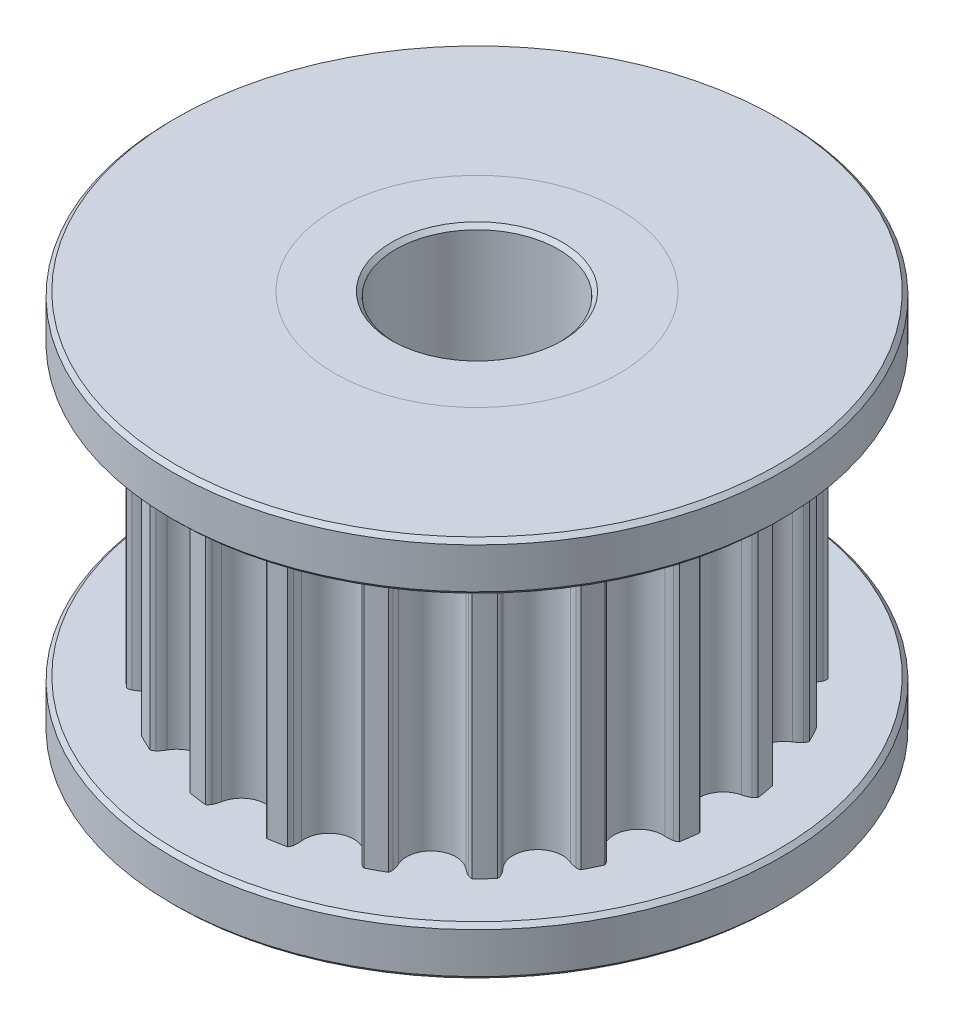
SolidWorks part; units mm, degrees
material "7075-T6 (SN)"
ref_plane "Přední rovina" through (0, 0, 0) normal (0, 0, 1) x (1, 0, 0)
ref_plane "Horní rovina" through (0, 0, 0) normal (0, 1, 0) x (1, 0, 0)
ref_plane "Pravá rovina" through (0, 0, 0) normal (1, 0, 0) x (0, 0, -1)
sketch "Skica1" plane through (0, 0, 0) normal (0, 1, 0) x (1, 0, 0)
  circle A0 centre (0, 0) radius 2
  arc B0 (-5.7301, 1.0983) -> (-5.3872, 2.2403) centre (-5.6803, 1.7058) ccw
  arc B1 (-5.7301, 1.0983) -> (-5.922, 1.0859) centre (-5.7841, 0.4401) ccw
  arc B2 (-5.922, 1.0859) -> (-6.0197, 1.0387) centre (-5.8743, 0.8624) ccw
  arc B3 (-6.0197, 1.0387) -> (-6.0791, 0.6004) centre (0, 0) ccw
  arc B4 (-6.0791, 0.6004) -> (-5.9974, 0.5289) centre (-5.892, 0.7317) ccw
  arc B5 (-5.9974, 0.5289) -> (-5.8158, 0.466) centre (-5.6927, 1.1148) ccw
  arc B6 (-5.7891, -0.7262) -> (-5.8158, 0.466) centre (-5.9294, -0.133) ccw
  arc B7 (-5.7891, -0.7262) -> (-5.9677, -0.7972) centre (-5.637, -1.3689) ccw
  arc B8 (-5.9677, -0.7972) -> (-6.0461, -0.8723) centre (-5.8532, -0.9951) ccw
  arc B9 (-6.0461, -0.8723) -> (-5.9671, -1.3075) centre (0, 0) ccw
  arc B10 (-5.9671, -1.3075) -> (-5.8673, -1.3503) centre (-5.8297, -1.1248) ccw
  arc B11 (-5.8673, -1.3503) -> (-5.6751, -1.354) centre (-5.7586, -0.6989) ccw
  arc B12 (-5.2813, -2.4796) -> (-5.6751, -1.354) centre (-5.5981, -1.9587) ccw
  arc B13 (-5.2813, -2.4796) -> (-5.4293, -2.6023) centre (-4.9381, -3.0438) ccw
  arc B14 (-5.4293, -2.6023) -> (-5.4806, -2.698) centre (-5.2593, -2.7551) ccw
  arc B15 (-5.4806, -2.698) -> (-5.271, -3.0875) centre (0, 0) ccw
  arc B16 (-5.271, -3.0875) -> (-5.1629, -3.0973) centre (-5.1968, -2.8713) ccw
  arc B17 (-5.1629, -3.0973) -> (-4.979, -3.0415) centre (-5.2608, -2.4442) ccw
  arc B18 (-4.2566, -3.9902) -> (-4.979, -3.0415) centre (-4.7188, -3.5928) ccw
  arc B19 (-4.2566, -3.9902) -> (-4.3594, -4.1527) centre (-3.7559, -4.4208) ccw
  arc B20 (-4.3594, -4.1527) -> (-4.3786, -4.2595) centre (-4.1505, -4.2455) ccw
  arc B21 (-4.3786, -4.2595) -> (-4.059, -4.5652) centre (0, 0) ccw
  arc B22 (-4.059, -4.5652) -> (-3.9531, -4.5412) centre (-4.0552, -4.3366) ccw
  arc B23 (-3.9531, -4.5412) -> (-3.7954, -4.4312) centre (-4.248, -3.9503) ccw
  arc B24 (-2.8152, -5.1103) -> (-3.7954, -4.4312) centre (-3.3776, -4.8751) ccw
  arc B25 (-2.8152, -5.1103) -> (-2.8628, -5.2965) centre (-2.2059, -5.3651) ccw
  arc B26 (-2.8628, -5.2965) -> (-2.8481, -5.4041) centre (-2.6354, -5.3203) ccw
  arc B27 (-2.8481, -5.4041) -> (-2.4496, -5.596) centre (0, 0) ccw
  arc B28 (-2.4496, -5.596) -> (-2.3563, -5.5405) centre (-2.5166, -5.3775) ccw
  arc B29 (-2.3563, -5.5405) -> (-2.2403, -5.3872) centre (-2.8194, -5.0696) ccw
  arc B30 (-1.0983, -5.7301) -> (-2.2403, -5.3872) centre (-1.7058, -5.6803) ccw
  arc B31 (-1.0983, -5.7301) -> (-1.0859, -5.922) centre (-0.4401, -5.7841) ccw
  arc B32 (-1.0859, -5.922) -> (-1.0387, -6.0197) centre (-0.8624, -5.8743) ccw
  arc B33 (-1.0387, -6.0197) -> (-0.6004, -6.0791) centre (0, 0) ccw
  arc B34 (-0.6004, -6.0791) -> (-0.5289, -5.9974) centre (-0.7317, -5.892) ccw
  arc B35 (-0.5289, -5.9974) -> (-0.466, -5.8158) centre (-1.1148, -5.6927) ccw
  arc B36 (0.7262, -5.7891) -> (-0.466, -5.8158) centre (0.133, -5.9294) ccw
  arc B37 (0.7262, -5.7891) -> (0.7972, -5.9677) centre (1.3689, -5.637) ccw
  arc B38 (0.7972, -5.9677) -> (0.8723, -6.0461) centre (0.9951, -5.8532) ccw
  arc B39 (0.8723, -6.0461) -> (1.3075, -5.9671) centre (0, 0) ccw
  arc B40 (1.3075, -5.9671) -> (1.3503, -5.8673) centre (1.1248, -5.8297) ccw
  arc B41 (1.3503, -5.8673) -> (1.354, -5.6751) centre (0.6989, -5.7586) ccw
  arc B42 (2.4796, -5.2813) -> (1.354, -5.6751) centre (1.9587, -5.5981) ccw
  arc B43 (2.4796, -5.2813) -> (2.6023, -5.4293) centre (3.0438, -4.9381) ccw
  arc B44 (2.6023, -5.4293) -> (2.698, -5.4806) centre (2.7551, -5.2593) ccw
  arc B45 (2.698, -5.4806) -> (3.0875, -5.271) centre (0, 0) ccw
  arc B46 (3.0875, -5.271) -> (3.0973, -5.1629) centre (2.8713, -5.1968) ccw
  arc B47 (3.0973, -5.1629) -> (3.0415, -4.979) centre (2.4442, -5.2608) ccw
  arc B48 (3.9902, -4.2566) -> (3.0415, -4.979) centre (3.5928, -4.7188) ccw
  arc B49 (3.9902, -4.2566) -> (4.1527, -4.3594) centre (4.4208, -3.7559) ccw
  arc B50 (4.1527, -4.3594) -> (4.2595, -4.3786) centre (4.2455, -4.1505) ccw
  arc B51 (4.2595, -4.3786) -> (4.5652, -4.059) centre (0, 0) ccw
  arc B52 (4.5652, -4.059) -> (4.5412, -3.9531) centre (4.3366, -4.0552) ccw
  arc B53 (4.5412, -3.9531) -> (4.4312, -3.7954) centre (3.9503, -4.248) ccw
  arc B54 (5.1103, -2.8152) -> (4.4312, -3.7954) centre (4.8751, -3.3776) ccw
  arc B55 (5.1103, -2.8152) -> (5.2965, -2.8628) centre (5.3651, -2.2059) ccw
  arc B56 (5.2965, -2.8628) -> (5.4041, -2.8481) centre (5.3203, -2.6354) ccw
  arc B57 (5.4041, -2.8481) -> (5.596, -2.4496) centre (0, 0) ccw
  arc B58 (5.596, -2.4496) -> (5.5405, -2.3563) centre (5.3775, -2.5166) ccw
  arc B59 (5.5405, -2.3563) -> (5.3872, -2.2403) centre (5.0696, -2.8194) ccw
  arc B60 (5.7301, -1.0983) -> (5.3872, -2.2403) centre (5.6803, -1.7058) ccw
  arc B61 (5.7301, -1.0983) -> (5.922, -1.0859) centre (5.7841, -0.4401) ccw
  arc B62 (5.922, -1.0859) -> (6.0197, -1.0387) centre (5.8743, -0.8624) ccw
  arc B63 (6.0197, -1.0387) -> (6.0791, -0.6004) centre (0, 0) ccw
  arc B64 (6.0791, -0.6004) -> (5.9974, -0.5289) centre (5.892, -0.7317) ccw
  arc B65 (5.9974, -0.5289) -> (5.8158, -0.466) centre (5.6927, -1.1148) ccw
  arc B66 (5.7891, 0.7262) -> (5.8158, -0.466) centre (5.9294, 0.133) ccw
  arc B67 (5.7891, 0.7262) -> (5.9677, 0.7972) centre (5.637, 1.3689) ccw
  arc B68 (5.9677, 0.7972) -> (6.0461, 0.8723) centre (5.8532, 0.9951) ccw
  arc B69 (6.0461, 0.8723) -> (5.9671, 1.3075) centre (0, 0) ccw
  arc B70 (5.9671, 1.3075) -> (5.8673, 1.3503) centre (5.8297, 1.1248) ccw
  arc B71 (5.8673, 1.3503) -> (5.6751, 1.354) centre (5.7586, 0.6989) ccw
  arc B72 (5.2813, 2.4796) -> (5.6751, 1.354) centre (5.5981, 1.9587) ccw
  arc B73 (5.2813, 2.4796) -> (5.4293, 2.6023) centre (4.9381, 3.0438) ccw
  arc B74 (5.4293, 2.6023) -> (5.4806, 2.698) centre (5.2593, 2.7551) ccw
  arc B75 (5.4806, 2.698) -> (5.271, 3.0875) centre (0, 0) ccw
  arc B76 (5.271, 3.0875) -> (5.1629, 3.0973) centre (5.1968, 2.8713) ccw
  arc B77 (5.1629, 3.0973) -> (4.979, 3.0415) centre (5.2608, 2.4442) ccw
  arc B78 (4.2566, 3.9902) -> (4.979, 3.0415) centre (4.7188, 3.5928) ccw
  arc B79 (4.2566, 3.9902) -> (4.3594, 4.1527) centre (3.7559, 4.4208) ccw
  arc B80 (4.3594, 4.1527) -> (4.3786, 4.2595) centre (4.1505, 4.2455) ccw
  arc B81 (4.3786, 4.2595) -> (4.059, 4.5652) centre (0, 0) ccw
  arc B82 (4.059, 4.5652) -> (3.9531, 4.5412) centre (4.0552, 4.3366) ccw
  arc B83 (3.9531, 4.5412) -> (3.7954, 4.4312) centre (4.248, 3.9503) ccw
  arc B84 (2.8152, 5.1103) -> (3.7954, 4.4312) centre (3.3776, 4.8751) ccw
  arc B85 (2.8152, 5.1103) -> (2.8628, 5.2965) centre (2.2059, 5.3651) ccw
  arc B86 (2.8628, 5.2965) -> (2.8481, 5.4041) centre (2.6354, 5.3203) ccw
  arc B87 (2.8481, 5.4041) -> (2.4496, 5.596) centre (0, 0) ccw
  arc B88 (2.4496, 5.596) -> (2.3563, 5.5405) centre (2.5166, 5.3775) ccw
  arc B89 (2.3563, 5.5405) -> (2.2403, 5.3872) centre (2.8194, 5.0696) ccw
  arc B90 (1.0983, 5.7301) -> (2.2403, 5.3872) centre (1.7058, 5.6803) ccw
  arc B91 (1.0983, 5.7301) -> (1.0859, 5.922) centre (0.4401, 5.7841) ccw
  arc B92 (1.0859, 5.922) -> (1.0387, 6.0197) centre (0.8624, 5.8743) ccw
  arc B93 (1.0387, 6.0197) -> (0.6004, 6.0791) centre (0, 0) ccw
  arc B94 (0.6004, 6.0791) -> (0.5289, 5.9974) centre (0.7317, 5.892) ccw
  arc B95 (0.5289, 5.9974) -> (0.466, 5.8158) centre (1.1148, 5.6927) ccw
  arc B96 (-0.7262, 5.7891) -> (0.466, 5.8158) centre (-0.133, 5.9294) ccw
  arc B97 (-0.7262, 5.7891) -> (-0.7972, 5.9677) centre (-1.3689, 5.637) ccw
  arc B98 (-0.7972, 5.9677) -> (-0.8723, 6.0461) centre (-0.9951, 5.8532) ccw
  arc B99 (-0.8723, 6.0461) -> (-1.3075, 5.9671) centre (0, 0) ccw
  arc B100 (-1.3075, 5.9671) -> (-1.3503, 5.8673) centre (-1.1248, 5.8297) ccw
  arc B101 (-1.3503, 5.8673) -> (-1.354, 5.6751) centre (-0.6989, 5.7586) ccw
  arc B102 (-2.4796, 5.2813) -> (-1.354, 5.6751) centre (-1.9587, 5.5981) ccw
  arc B103 (-2.4796, 5.2813) -> (-2.6023, 5.4293) centre (-3.0438, 4.9381) ccw
  arc B104 (-2.6023, 5.4293) -> (-2.698, 5.4806) centre (-2.7551, 5.2593) ccw
  arc B105 (-2.698, 5.4806) -> (-3.0875, 5.271) centre (0, 0) ccw
  arc B106 (-3.0875, 5.271) -> (-3.0973, 5.1629) centre (-2.8713, 5.1968) ccw
  arc B107 (-3.0973, 5.1629) -> (-3.0415, 4.979) centre (-2.4442, 5.2608) ccw
  arc B108 (-3.9902, 4.2566) -> (-3.0415, 4.979) centre (-3.5928, 4.7188) ccw
  arc B109 (-3.9902, 4.2566) -> (-4.1527, 4.3594) centre (-4.4208, 3.7559) ccw
  arc B110 (-4.1527, 4.3594) -> (-4.2595, 4.3786) centre (-4.2455, 4.1505) ccw
  arc B111 (-4.2595, 4.3786) -> (-4.5652, 4.059) centre (0, 0) ccw
  arc B112 (-4.5652, 4.059) -> (-4.5412, 3.9531) centre (-4.3366, 4.0552) ccw
  arc B113 (-4.5412, 3.9531) -> (-4.4312, 3.7954) centre (-3.9503, 4.248) ccw
  arc B114 (-5.1103, 2.8152) -> (-4.4312, 3.7954) centre (-4.8751, 3.3776) ccw
  arc B115 (-5.1103, 2.8152) -> (-5.2965, 2.8628) centre (-5.3651, 2.2059) ccw
  arc B116 (-5.2965, 2.8628) -> (-5.4041, 2.8481) centre (-5.3203, 2.6354) ccw
  arc B117 (-5.4041, 2.8481) -> (-5.596, 2.4496) centre (0, 0) ccw
  arc B118 (-5.596, 2.4496) -> (-5.5405, 2.3563) centre (-5.3775, 2.5166) ccw
  arc B119 (-5.5405, 2.3563) -> (-5.3872, 2.2403) centre (-5.0696, 2.8194) ccw
  dimension "D1" = 4
sketch_block_instance "Blok1-1"
sketch_block "Blok1"
extrude "Přidat vysunutím1" add sketch "Skica1" along normal blind 7 from offset 7.8
sketch "Skica2" plane through (0, 7.8, 0) normal (0, -1, 0) x (1, 0, 0)
  circle A0 centre (0, 0) radius 3.5
  circle A1 centre (0, 0) radius 2 construction
  circle A2 centre (0, 0) radius 2
  dimension "D1" = 7
extrude "Přidat vysunutím2" add sketch "Skica2" along normal blind 7.8
sketch "Skica3" plane through (0, 14.8, 0) normal (0, 1, 0) x (1, 0, 0)
  circle A0 centre (0, 0) radius 3.5
  circle A1 centre (0, 0) radius 2 construction
  circle A2 centre (0, 0) radius 2
  dimension "D1" = 7
extrude "Přidat vysunutím3" add sketch "Skica3" along normal blind 1.2
sketch "Skica5" plane through (0, 16, 0) normal (0, 1, 0) x (1, 0, 0)
  circle A0 centre (0, 0) radius 7.5
  circle A3 centre (0, 0) radius 3.5 construction
  circle A4 centre (0, 0) radius 3.5
  dimension "D1" = 15
extrude "Přidat vysunutím4" add sketch "Skica5" against normal up to surface (1.2 mm away) separate body up to face at (0, 14.8, 0)
sketch "Skica6" plane through (0, 0, 0) normal (0, -1, 0) x (1, 0, 0)
  circle A0 centre (0, 0) radius 7.5
  circle A1 centre (0, 0) radius 3.5 construction
  circle A2 centre (0, 0) radius 3.5
  circle A3 centre (0, 0) radius 7.5 construction
extrude "Přidat vysunutím5" add sketch "Skica6" against normal up to surface (7.8 mm away) separate body up to face at (0, 7.8, 0)
hole_wizard "M4 závit1" positions "3DSkica2" profile "Skica8" tap size "M4" standard "ISO"
sketch3d "3DSkica2"
  line L0 (0, 0, 7.5) -> (0, 3.9, 7.5) construction
  line L1 (7.5, 0, 0) -> (7.5, 3.9, 0) construction
  circle A0 centre (0, 0, 0) radius 7.5 construction
  point P0 (0, 3.9, 7.5)
  point P2 (7.5, 3.9, 0)
  point P34 (0, -7.5, 0)
  dimension "D1" = 3.9
sketch "Skica8" plane through (0, 3.9, 7.5) normal (1, 0, 0) x (0, -1, 0)
  line L0 (0, 0) -> (0, 11)
  line L1 (0, 11) -> (1.65, 11)
  line L2 (1.65, 11) -> (1.65, 0)
  line L5 (1.65, 0) -> (0, 0)
  line L11 (0, -6.35) -> (0, 107.95) construction
  dimension "Průměr závitníku" = 3.3
  dimension "Hloubka závitníku" = 11
cosmetic thread "Závit díry1" parameters "D2"=4
cosmetic thread "Závit díry2" parameters "D2"=4
chamfer "Zkosení1" distance 0.1 angle 45 2 edges at (0, 14.8, 7.5) (0, 16, 7.5)
chamfer "Zkosení2" distance 0.1 angle 45 2 edges at (0, 0, -2) (0, 16, 2)
chamfer "Zkosení3" distance 0.1 angle 45 2 edges at (0, 0, -7.5) (0, 7.8, 7.5)
sketch "Sketch1" plane through (0, 0, 0) normal (0, -1, 0) x (1, 0, 0)
  circle A0 centre (0, 0) radius 7.5 construction
  circle A1 centre (0, 0) radius 7.5
extrude "Cut-Extrude1" cut sketch "Sketch1" against normal offset from surface (6.6 mm away) 1.2
chamfer "Chamfer1" distance 0.1 angle 45 1 edges at (0, 6.6, 7.5)
